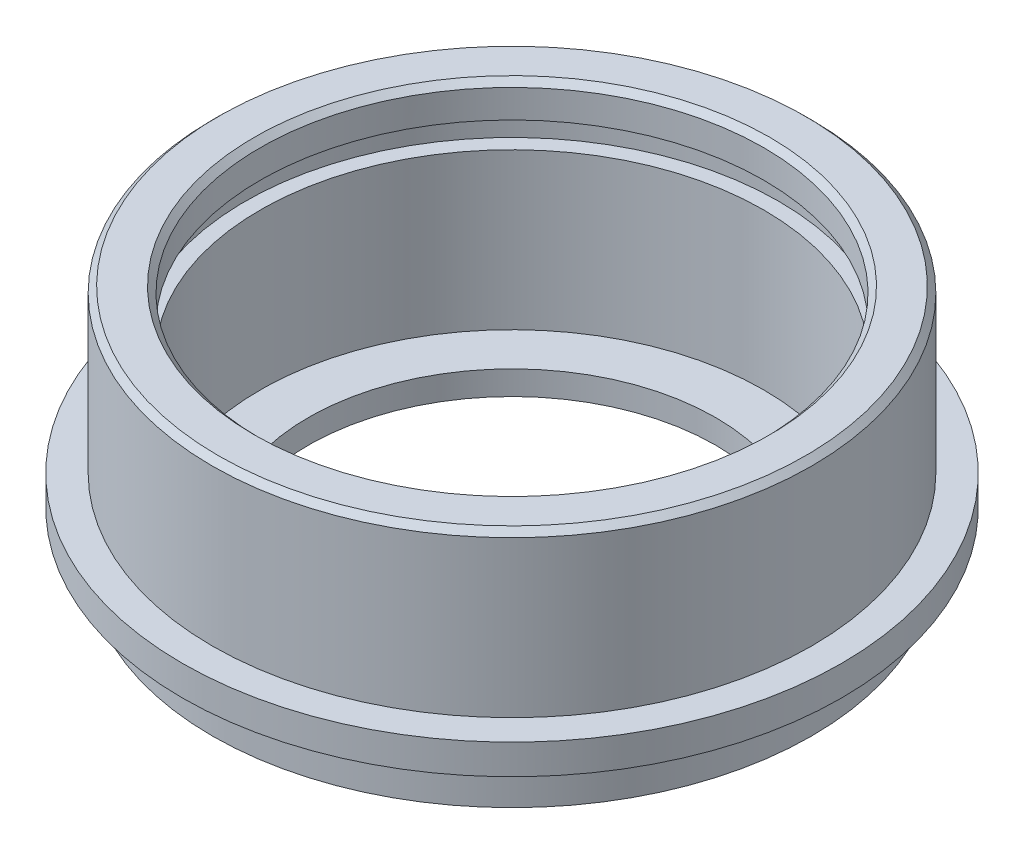
SolidWorks part; units mm, degrees
material " 09Г2С ГОСТ 4543-71"
ref_plane "Спереди" through (0, 0, 0) normal (0, 0, 1) x (1, 0, 0)
ref_plane "Сверху" through (0, 0, 0) normal (0, 1, 0) x (1, 0, 0)
ref_plane "Слева" through (0, 0, 0) normal (1, 0, 0) x (0, 0, -1)
sketch "Эскиз1" plane through (0, 0, 0) normal (0, 0, 1) x (1, 0, 0)
  line L0 (0, 0) -> (0, 79.6052) construction
  line L1 (17, 0) -> (17, 2)
  line L2 (17, 2) -> (21, 2)
  line L3 (21, 2) -> (21, 15)
  line L4 (21, 15) -> (22.25, 15)
  line L5 (22.25, 15) -> (22.25, 17.15)
  line L6 (22.25, 17.15) -> (21, 17.15)
  line L7 (21, 17.15) -> (21, 20)
  line L8 (21, 20) -> (25, 20)
  line L9 (25, 20) -> (25, 6.5)
  line L10 (25, 6.5) -> (27.5, 6.5)
  line L11 (27.5, 6.5) -> (27.5, 4)
  line L12 (27.5, 4) -> (25, 4)
  line L13 (25, 4) -> (25, 0)
  line L14 (25, 0) -> (17, 0)
  dimension "D1" = 4
  dimension "D2" = 2.5
  dimension "D3" = 2.5
  dimension "D4" = 4
  dimension "D5" = 2
  dimension "D6" = 20
  dimension "D7" = 2.15
  dimension "D8" = 13
  dimension "D9" = 34
  dimension "D10" = 42
  dimension "D11" = 44.5
  dimension "D12" = 2.85
  dimension "D13" = 50
revolve "Повернуть1" add sketch "Эскиз1" angle 360 about L0
chamfer "Фаска1" distance 0.5 angle 45 2 edges at (0, 20, -25) (0, 20, -21)
